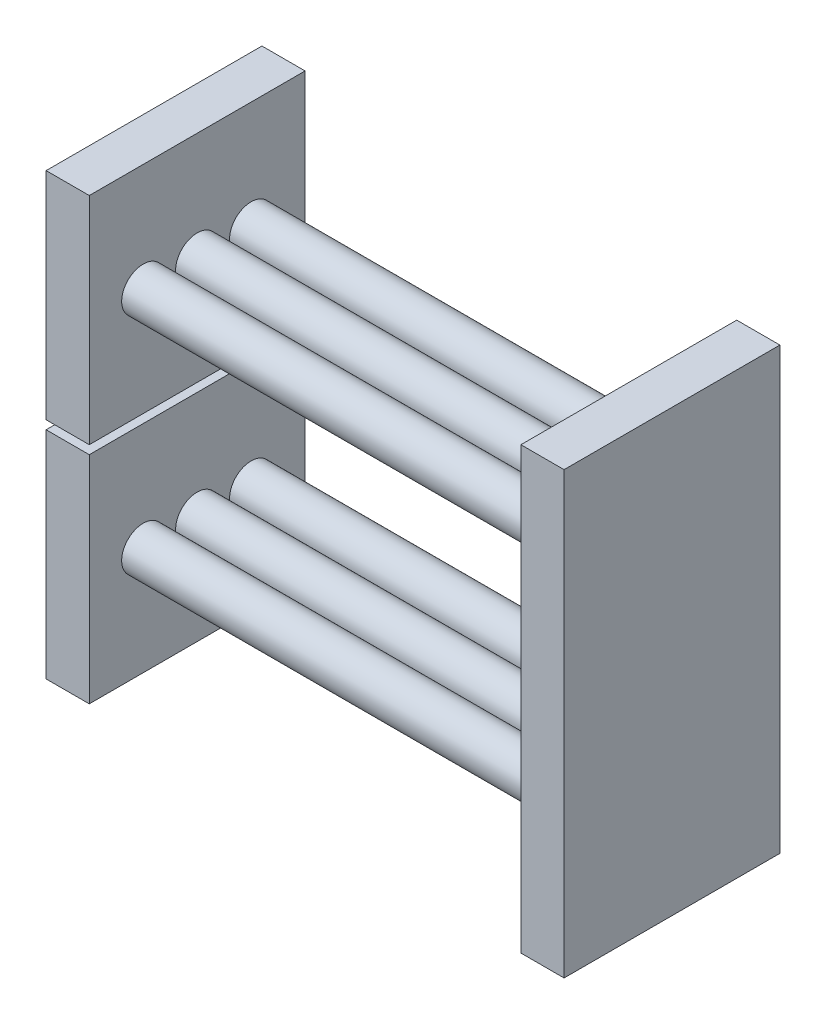
SolidWorks part; units mm, degrees
ref_plane "Front Plane" through (0, 0, 0) normal (0, 0, 1) x (1, 0, 0)
ref_plane "Top Plane" through (0, 0, 0) normal (0, 1, 0) x (1, 0, 0)
ref_plane "Right Plane" through (0, 0, 0) normal (1, 0, 0) x (0, 0, -1)
sketch "baseplatesketch" plane through (0, 0, 0) normal (1, 0, 0) x (0, 0, -1)
  line L1 (25, -25) -> (-25, -25)
  line L2 (25, -25) -> (25, 25)
  line L3 (25, 25) -> (-25, 25)
  line L4 (-25, -25) -> (-25, 25)
  line L5 (25, -25) -> (-25, 25) construction
  line L6 (25, 25) -> (-25, -25) construction
  point P0 (0, 0)
  dimension "PlateLength" = 50
  dimension "PlateWidth" = 50
extrude "Boss-Extrude1" add sketch "baseplatesketch" along normal blind 10 contours L1 L4 L3 L2
sketch "Sketch2" plane through (10, 0, 0) normal (1, 0, 0) x (0, 0, -1)
  line L0 (-25, 0) -> (25, 0) construction
  line L1 (-25, -25) -> (-25, 25) construction
  line L2 (25, -25) -> (25, 25) construction
  line L3 (0, 25) -> (0, -25) construction
  line L4 (25, 25) -> (-25, 25) construction
  line L5 (25, -25) -> (-25, -25) construction
  circle A0 centre (0, 0) radius 5
  point P9 (-12.5, 0)
  point P10 (12.5, 0)
  point P11 (0, 12.5)
  point P18 (0, -12.5)
  dimension "tubediameter" = 10
  dimension "SpacingLH" = 12.5
  dimension "SpacingRH" = 12.5
  dimension "SpacingTo" = 12.5
  dimension "SpacingBo" = 12.5
extrude "Boss-Extrude3" add sketch "Sketch2" along normal blind 100
sketch "minmax" plane through (10, 0, 0) normal (1, 0, 0) x (0, 0, -1)
  line L0 (0, 25) -> (0, -25) construction
  line L1 (25, 25) -> (-25, 25) construction
  line L2 (25, -25) -> (-25, -25) construction
  line L3 (23.5, 25) -> (23.5, -25) construction
  line L4 (-23.5, 25) -> (-23.5, -25) construction
  line L5 (-22, 25) -> (-22, -25) construction
  line L6 (22, 25) -> (22, -25) construction
  line L7 (-25, 0) -> (25, 0) construction
  line L8 (-25, -25) -> (-25, 25) construction
  line L9 (25, -25) -> (25, 25) construction
  line L10 (-25, 22) -> (25, 22)
  line L11 (-25, -22) -> (25, -22)
  line L12 (-25, 23.5) -> (25, 23.5)
  line L13 (-25, -23.5) -> (25, -23.5)
  dimension "MinEdgeLenwise" = 1.5
  dimension "MaxEdgeLenwise" = 3
  dimension "MinEdgeWidwise" = 1.5
  dimension "MaxEdgeWidwise" = 3
sketch "Sketch5" plane through (0, 0, 0) normal (-1, 0, 0) x (0, 0, 1)
  line L0 (25, 0) -> (-25, 0) construction
  line L1 (0, 25) -> (0, -25) construction
  point P0 (0, 0)
  dimension "tubeoffset" = 0
pattern_linear "LPattern1" count 2 spacing 12.5 along (0, 0, -1) count 2 spacing 12.5 along (0, 0, 1) of "Boss-Extrude3"
pattern_linear "LPattern3" [suppressed] count 2 spacing 12.5 along (0, -1, 0) count 2 spacing 12.5 along (0, -1, 0)
ref_plane "Plane1" through (0, -26, 0) normal (0, -1, 0) x (-1, 0, 0)
sketch "Sketch7" plane through (110, 0, 0) normal (1, 0, 0) x (0, 0, -1)
  line L5 (-25, 25) -> (25, 25)
  line L6 (-25, 25) -> (-25, -26)
  line L7 (-25, -26) -> (25, -26)
  line L8 (25, 25) -> (25, -26)
  point P0 (0, 0)
  dimension "mixchamberlength" = 50
  dimension "mixchamberwidth" = 51
extrude "Boss-Extrude4" add sketch "Sketch7" along normal blind 10
mirror "Mirror8" about plane through (0, -26, 0) normal (0, -1, 0) of bodies 108
sketch "Sketch9" plane through (0, 0, 0) normal (-1, 0, 0) x (0, 0, 1)
  line L0 (-25, -25) -> (-25, 25) construction
  line L1 (-25, 25) -> (25, 25) construction
  circle A0 centre (5, 0) radius 10
  dimension "zoffset" = 30
  dimension "yoffset" = 25
sketch "Sketch10" plane through (0, 0, 0) normal (-1, 0, 0) x (0, 0, 1)
  line L0 (-25, -27) -> (-25, -77) construction
  line L1 (-25, -27) -> (25, -27) construction
  circle A0 centre (5, -47) radius 10
  dimension "zoffset_out" = 30
  dimension "yoffset_out" = 20
split line "Split Line1"
split line "Split Line2"
equation "\"tubeDia\"= 10"
equation "\"tubediameter@Sketch2\"= \"tubeDia\""
equation "\"FeatureSpacing\"= 12.5"
equation "\"MinEdgeToFeatureDistance\"= 1.5"
equation "\"MaxEdgeToFeatureDistance\"= 3"
equation "\"MinEdgeLenwise@minmax\" = \"MinEdgeToFeatureDistance\""
equation "\"MaxEdgeLenwise@minmax\" = \"MaxEdgeToFeatureDistance\""
equation "\"NetSpaceAvailable\"=  ( \"PlateLength@baseplatesketch\" -  ( 2 * \"MinEdgeToFeatureDistance\" )  - \"tubeDia\" ) "
equation "\"no-of-tubes\"= int ( \"NetSpaceAvailable\" / \"FeatureSpacing\" + 1 )"
equation "\"seedFeatureOffset\"= IIF ( int ( \"no-of-tubes\" / 2 ) < > ( \"no-of-tubes\" / 2 ) , 0 , \"FeatureSpacing\" / 2 )"
equation "\"left-tube-instances\"= IIF ( int ( \"no-of-tubes\" / 2 ) < > ( \"no-of-tubes\" / 2 ) , int ( \"no-of-tubes\" / 2 ) + 1 , int ( \"no-of-tubes\" / 2 ) )"
equation "\"right-tube-instances\"= int ( \"no-of-tubes\" / 2 + 1 )"
equation "\"SpacingLH@Sketch2\"=\"FeatureSpacing\""
equation "\"SpacingRH@Sketch2\"=\"FeatureSpacing\""
equation "\"D3@LPattern1\"=\"FeatureSpacing\""
equation "\"D1@LPattern1\"=\"right-tube-instances\""
equation "\"D4@LPattern1\"=\"FeatureSpacing\""
equation "\"D2@LPattern1\"= \"left-tube-instances\""
equation "\"SpacingTo@Sketch2\"=\"FeatureSpacing\""
equation "\"SpacingBo@Sketch2\"=\"FeatureSpacing\""
equation "\"MinEdgeWidwise@minmax\"= \"MinEdgeToFeatureDistance\""
equation "\"MaxEdgeWidwise@minmax\"= \"MaxEdgeToFeatureDistance\""
equation "\"NetSpaceAvailable-wid\"= ( \"PlateWidth@baseplatesketch\" - ( 2 * \"MinEdgeToFeatureDistance\" ) - \"tubeDia\" )"
equation "\"no-of-tubes-wid\"= int ( \"NetSpaceAvailable-wid\" / \"FeatureSpacing\" + 1 )"
equation "\"seedFeatureOffset-wid\"= IIF ( int ( \"no-of-tubes-wid\" / 2 ) < > ( \"no-of-tubes-wid\" / 2 ) , 0 , \"FeatureSpacing\" / 2 )"
equation "\"top-tube-instances\"= IIF ( int ( \"no-of-tubes-wid\" / 2 ) < > ( \"no-of-tubes-wid\" / 2 ) , int ( \"no-of-tubes-wid\" / 2 ) + 1 , int ( \"no-of-tubes-wid\" / 2 ) )"
equation "\"bottom-tube-instances\"= int ( \"no-of-tubes-wid\" / 2 + 1 )"
equation "\"D3@LPattern3\"=\"FeatureSpacing\""
equation "\"D1@LPattern3\"=\"top-tube-instances\""
equation "\"D4@LPattern3\"=\"FeatureSpacing\""
equation "\"D2@LPattern3\"=\"bottom-tube-instances\""
equation "\"manifold-length\"= 50"
equation "\"PlateLength@baseplatesketch\"= \"manifold-length\""
equation "\"manifold-width\"= 50"
equation "\"PlateWidth@baseplatesketch\"= \"manifold-width\""
equation "\"mixchamberlength@Sketch7\"=\"manifold-length\""
equation "\"mixchamberwidth@Sketch7\"=\"manifold-width\"+1"
equation "\"Zoffset-in\"= 30"
equation "\"Yoffset-in\"= 25"
equation "\"zoffset@Sketch9\"= \"Zoffset-in\""
equation "\"yoffset@Sketch9\"= \"Yoffset-in\""
equation "\"Zoffset-out\"= 30"
equation "\"Yoffset-out\"= 20"
equation "\"zoffset_out@Sketch10\"= \"Zoffset-out\""
equation "\"yoffset_out@Sketch10\"= \"Yoffset-out\""
equation "\"zoffset@Sketch9\" = \"Zoffset-in\""
equation "\"yoffset@Sketch9\" = \"Yoffset-in\""
